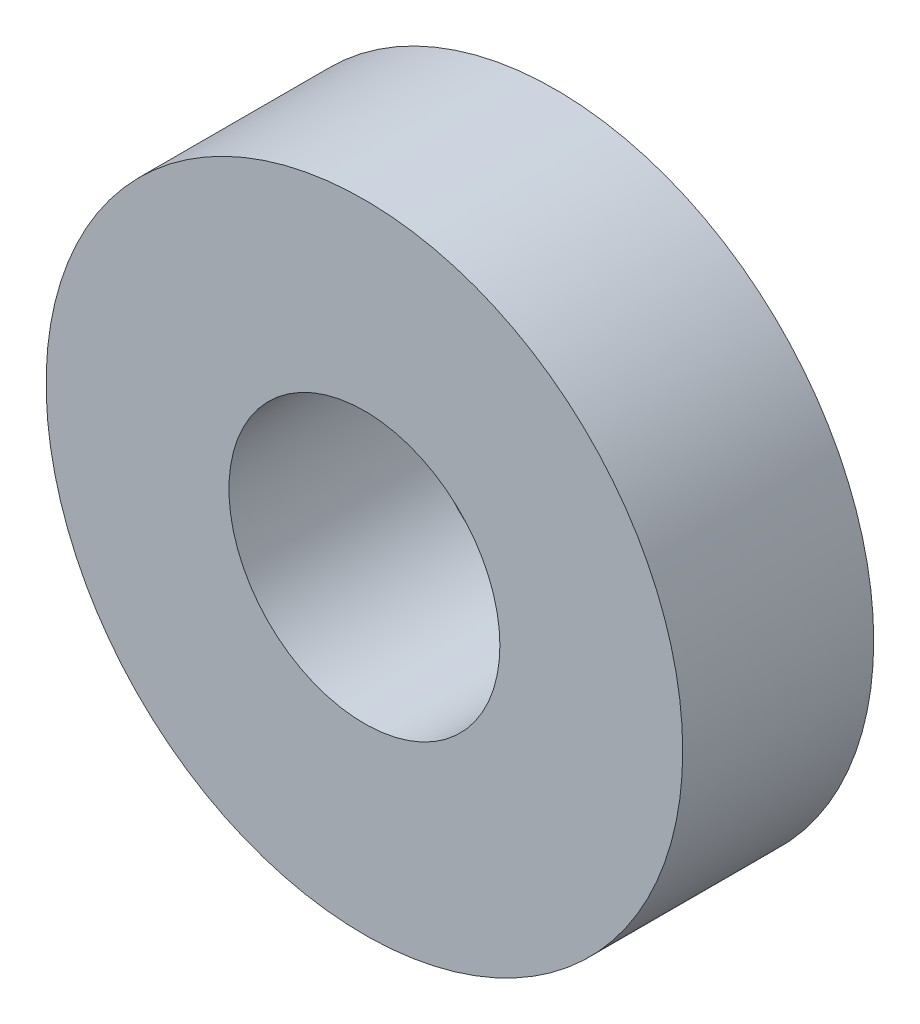
SolidWorks part; units mm, degrees
material "SS 304"
ref_plane "Front Plane" through (0, 0, 0) normal (0, 0, 1) x (1, 0, 0)
ref_plane "Top Plane" through (0, 0, 0) normal (0, 1, 0) x (1, 0, 0)
ref_plane "Right Plane" through (0, 0, 0) normal (1, 0, 0) x (0, 0, -1)
sketch "Sketch1" plane through (0, 0, 0) normal (0, 0, 1) x (1, 0, 0)
  circle A0 centre (0, 0) radius 7.9375
  dimension "D1" = 15.875
extrude "Boss-Extrude1" add sketch "Sketch1" along normal mid plane 4.7625
sketch "Sketch2" plane through (0, 0, 2.3813) normal (0, 0, 1) x (1, 0, 0)
  circle A0 centre (0, 0) radius 3.3782
  dimension "D1" = 6.7564
extrude "Cut-Extrude1" cut sketch "Sketch2" against normal up to next
